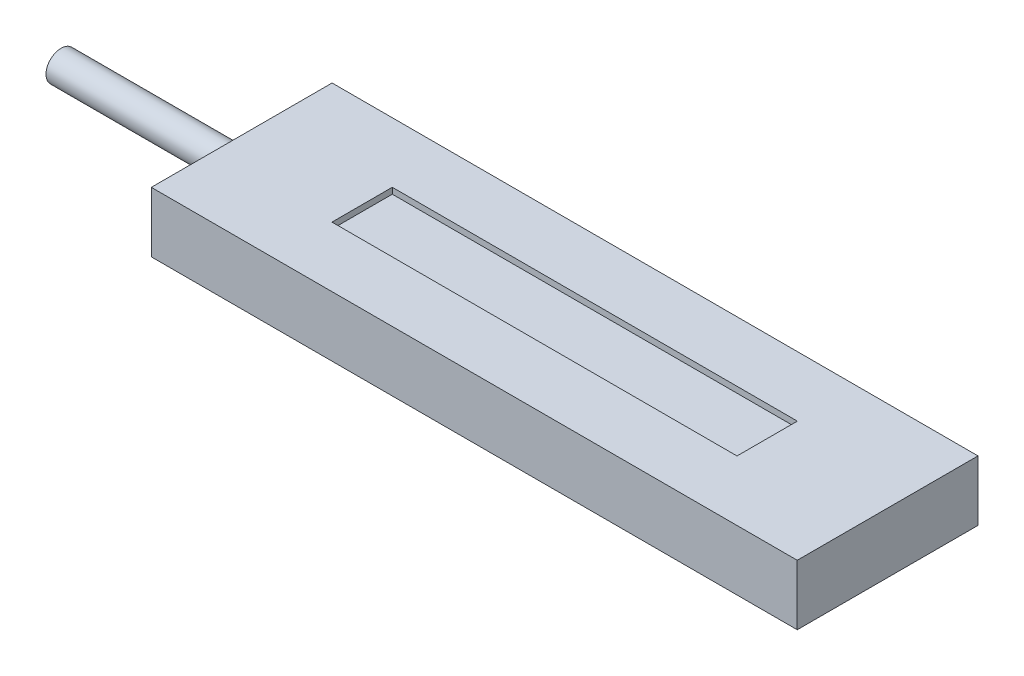
SolidWorks part; units mm, degrees
ref_plane "Front Plane" through (0, 0, 0) normal (0, 0, 1) x (1, 0, 0)
ref_plane "Top Plane" through (0, 0, 0) normal (0, 1, 0) x (1, 0, 0)
ref_plane "Right Plane" through (0, 0, 0) normal (1, 0, 0) x (0, 0, -1)
sketch "Sketch1" plane through (0, 0, 0) normal (0, 1, 0) x (1, 0, 0)
  line L1 (0, 0) -> (107.27, 0)
  line L2 (0, 0) -> (0, 30.02)
  line L3 (0, 30.02) -> (107.27, 30.02)
  line L4 (107.27, 0) -> (107.27, 30.02)
  dimension "D1" = 107.27
  dimension "D2" = 30.02
extrude "Boss-Extrude1" add sketch "Sketch1" along normal blind 10
sketch "Sketch2" plane through (0, 0, 0) normal (-1, 0, 0) x (0, 0, 1)
  line L0 (-30.02, 10) -> (0, 0) construction
  circle A0 centre (-15.01, 5) radius 2.5
  dimension "D1" = 5
extrude "Boss-Extrude2" add sketch "Sketch2" along normal blind 30
sketch "Sketch3" plane through (0, 10, 0) normal (0, 1, 0) x (1, 0, 0)
  line L0 (0, 30.02) -> (0, 0) construction
  line L1 (20, 20.02) -> (87.27, 20.02)
  line L2 (20, 20.02) -> (20, 10)
  line L3 (20, 10) -> (87.27, 10)
  line L4 (87.27, 20.02) -> (87.27, 10)
  line L5 (107.27, 0) -> (107.27, 30.02) construction
  line L6 (107.27, 30.02) -> (0, 30.02) construction
  line L7 (0, 0) -> (107.27, 0) construction
  point P4 (20.9426, 19.1821)
  dimension "D1" = 20
  dimension "D2" = 20
  dimension "D3" = 10
  dimension "D4" = 10
extrude "Cut-Extrude1" cut sketch "Sketch3" against normal blind 1
